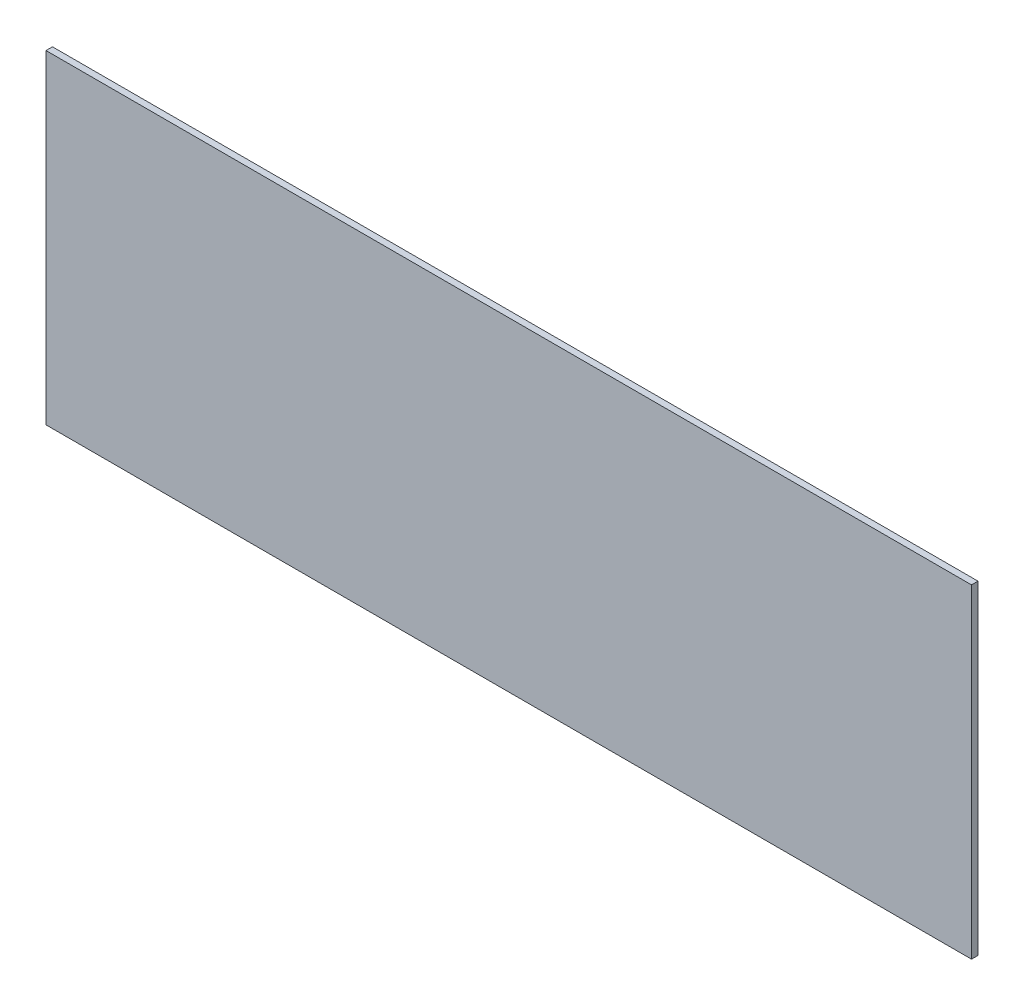
SolidWorks part; units mm, degrees
ref_plane "Front Plane" through (0, 0, 0) normal (0, 0, 1) x (1, 0, 0)
ref_plane "Top Plane" through (0, 0, 0) normal (0, 1, 0) x (1, 0, 0)
ref_plane "Right Plane" through (0, 0, 0) normal (1, 0, 0) x (0, 0, -1)
sketch "Sketch1" plane through (0, 0, 0) normal (0, 0, 1) x (1, 0, 0)
  line L1 (-142.75, 50) -> (142.75, 50)
  line L2 (-142.75, 50) -> (-142.75, -50)
  line L3 (-142.75, -50) -> (142.75, -50)
  line L4 (142.75, 50) -> (142.75, -50)
  line L5 (-142.75, 50) -> (142.75, -50) construction
  line L6 (-142.75, -50) -> (142.75, 50) construction
  point P0 (0, 0)
  dimension "D1" = 285.5
  dimension "D2" = 100
extrude "Boss-Extrude1" add sketch "Sketch1" along normal blind 2
